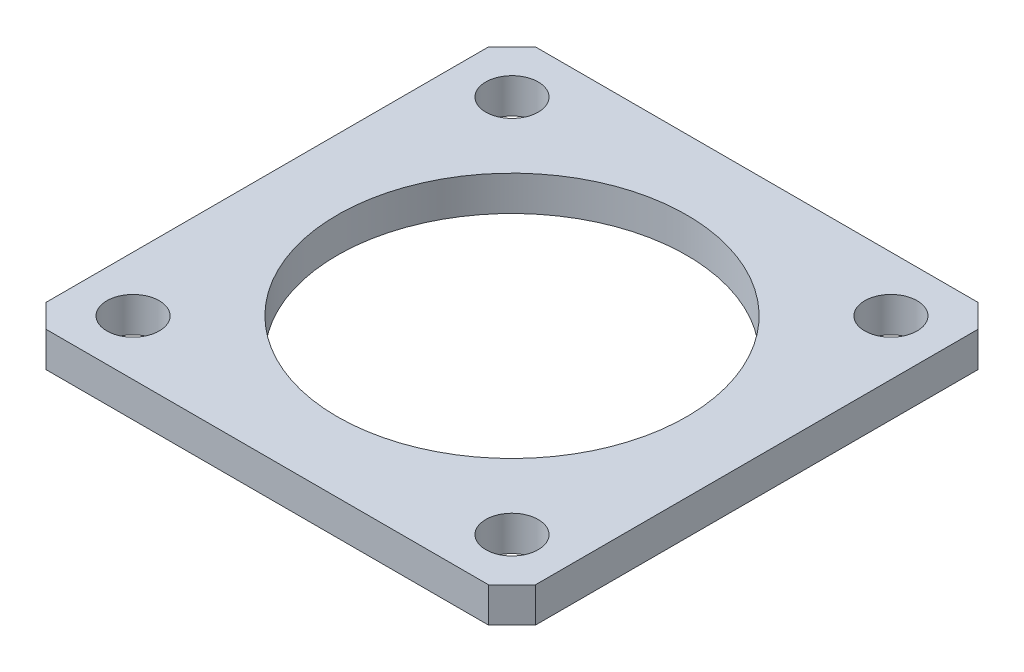
SolidWorks part; units mm, degrees
ref_plane "Front Plane" through (0, 0, 0) normal (0, 0, 1) x (1, 0, 0)
ref_plane "Top Plane" through (0, 0, 0) normal (0, 1, 0) x (1, 0, 0)
ref_plane "Right Plane" through (0, 0, 0) normal (1, 0, 0) x (0, 0, -1)
sketch "Sketch1" plane through (0, 0, 0) normal (0, 1, 0) x (1, 0, 0)
  line L0 (19, 21) -> (21, 19)
  line L1 (-19, 21) -> (19, 21)
  line L2 (-21, 19) -> (-21, -19)
  line L3 (-19, -21) -> (19, -21)
  line L4 (21, 19) -> (21, -19)
  line L5 (-21, 21) -> (21, -21) construction
  line L6 (-21, -21) -> (21, 21) construction
  line L7 (-19, 21) -> (-21, 19)
  line L8 (-21, -19) -> (-19, -21)
  line L9 (21, -19) -> (19, -21)
  circle A0 centre (0, 0) radius 23 construction
  circle A1 centre (-16.2635, 16.2635) radius 2.25
  circle A2 centre (16.2635, 16.2635) radius 2.25
  circle A3 centre (16.2635, -16.2635) radius 2.25
  circle A4 centre (-16.2635, -16.2635) radius 2.25
  circle A5 centre (0, 0) radius 15
  point P0 (0, 0)
  dimension "D3" = 46
  dimension "D4" = 4.5
  dimension "D6" = 30
  dimension "D1" = 42
  dimension "D2" = 42
extrude "Boss-Extrude1" add sketch "Sketch1" along normal blind 3
